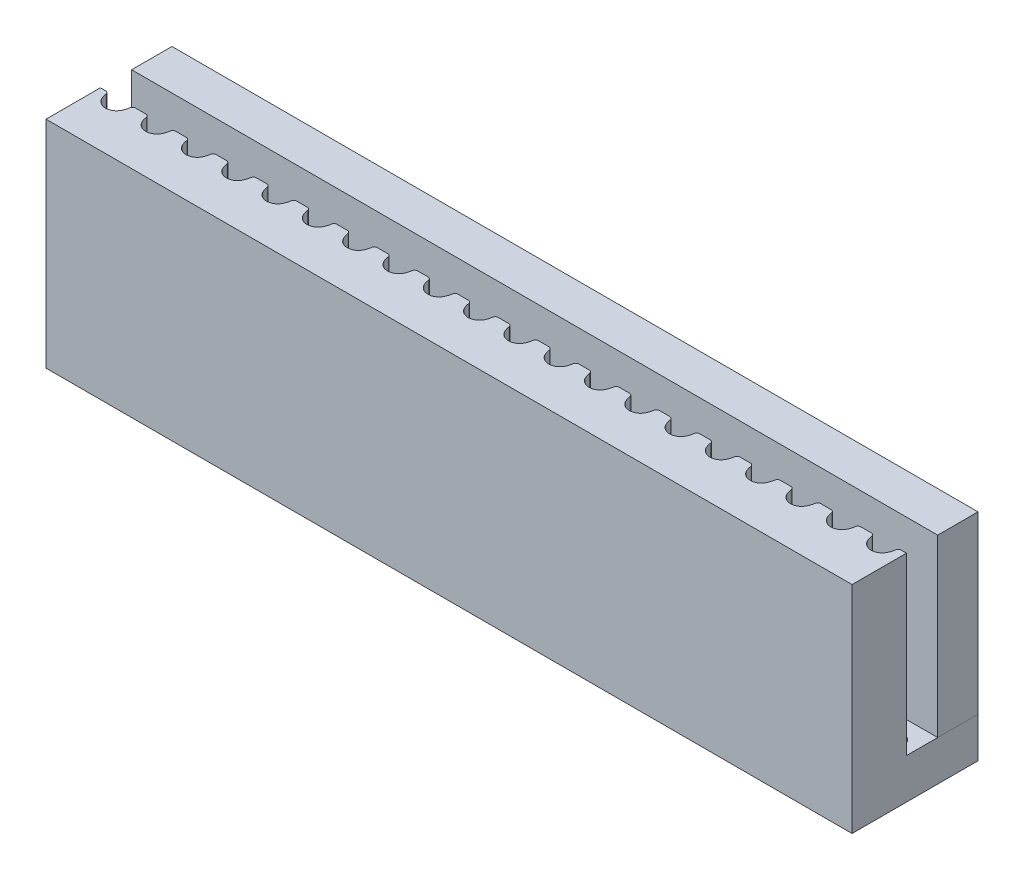
SolidWorks part; units mm, degrees
ref_plane "Front Plane" through (0, 0, 0) normal (0, 0, 1) x (1, 0, 0)
ref_plane "Top Plane" through (0, 0, 0) normal (0, 1, 0) x (1, 0, 0)
ref_plane "Right Plane" through (0, 0, 0) normal (1, 0, 0) x (0, 0, -1)
sketch "Sketch1" plane through (0, 0, 0) normal (0, 1, 0) x (1, 0, 0)
  line L0 (-20, 0.95) -> (20, 0.95) construction
  line L1 (0, -55) -> (0, 55) construction
  line L2 (-55, 0) -> (55, 0) construction
  line L3 (-20, 0.32) -> (20, 0.32)
  line L4 (-20, -0.43) -> (20, -0.43) construction
  line L5 (-19, 1.863) -> (-19, -1.7327) construction
  line L6 (-18.6, 1.863) -> (-18.6, -1.7327) construction
  line L7 (-20.453, 0.574) -> (20.5239, 0.574) construction
  line L8 (-19.4, 1.863) -> (-19.4, -1.7327) construction
  line L11 (-19.5915, 0.1896) -> (-17.5915, 0.1896) construction
  line L12 (20, 0.32) -> (20, -2.38)
  line L13 (20, -2.38) -> (-20, -2.38)
  line L14 (-20, -2.38) -> (-20, 0.32)
  line L17 (20, 1.87) -> (-20, 1.87)
  line L18 (20, 1.87) -> (20, 3.87)
  line L19 (20, 3.87) -> (-20, 3.87)
  line L20 (-20, 1.87) -> (-20, 3.87)
  circle A0 centre (-19, 0.125) radius 0.555
  arc A3 (-19.5915, 0.1896) -> (-19.7402, 0.32) centre (-19.7402, 0.17) ccw
  arc A4 (-18.2598, 0.32) -> (-18.4085, 0.1896) centre (-18.2598, 0.17) ccw
  arc A5 (-19.5915, 0.1896) -> (-19.4989, -0.1182) centre (-18.6, 0.32) ccw
  arc A6 (-18.5011, -0.1182) -> (-18.4085, 0.1896) centre (-19.4, 0.32) ccw
  arc A7 (-17.5915, 0.1896) -> (-17.7402, 0.32) centre (-17.7402, 0.17) ccw
  arc A8 (-17.5915, 0.1896) -> (-17.4989, -0.1182) centre (-16.6, 0.32) ccw
  circle A9 centre (-17, 0.125) radius 0.555
  arc A10 (-16.2598, 0.32) -> (-16.4085, 0.1896) centre (-16.2598, 0.17) ccw
  arc A11 (-16.5011, -0.1182) -> (-16.4085, 0.1896) centre (-17.4, 0.32) ccw
  arc A12 (-15.5915, 0.1896) -> (-15.7402, 0.32) centre (-15.7402, 0.17) ccw
  arc A13 (-15.5915, 0.1896) -> (-15.4989, -0.1182) centre (-14.6, 0.32) ccw
  circle A14 centre (-15, 0.125) radius 0.555
  arc A15 (-14.2598, 0.32) -> (-14.4085, 0.1896) centre (-14.2598, 0.17) ccw
  arc A16 (-14.5011, -0.1182) -> (-14.4085, 0.1896) centre (-15.4, 0.32) ccw
  arc A17 (-13.5915, 0.1896) -> (-13.7402, 0.32) centre (-13.7402, 0.17) ccw
  arc A18 (-13.5915, 0.1896) -> (-13.4989, -0.1182) centre (-12.6, 0.32) ccw
  circle A19 centre (-13, 0.125) radius 0.555
  arc A20 (-12.2598, 0.32) -> (-12.4085, 0.1896) centre (-12.2598, 0.17) ccw
  arc A21 (-12.5011, -0.1182) -> (-12.4085, 0.1896) centre (-13.4, 0.32) ccw
  arc A22 (-11.5915, 0.1896) -> (-11.7402, 0.32) centre (-11.7402, 0.17) ccw
  arc A23 (-11.5915, 0.1896) -> (-11.4989, -0.1182) centre (-10.6, 0.32) ccw
  circle A24 centre (-11, 0.125) radius 0.555
  arc A25 (-10.2598, 0.32) -> (-10.4085, 0.1896) centre (-10.2598, 0.17) ccw
  arc A26 (-10.5011, -0.1182) -> (-10.4085, 0.1896) centre (-11.4, 0.32) ccw
  arc A27 (-9.5915, 0.1896) -> (-9.7402, 0.32) centre (-9.7402, 0.17) ccw
  arc A28 (-9.5915, 0.1896) -> (-9.4989, -0.1182) centre (-8.6, 0.32) ccw
  circle A29 centre (-9, 0.125) radius 0.555
  arc A30 (-8.2598, 0.32) -> (-8.4085, 0.1896) centre (-8.2598, 0.17) ccw
  arc A31 (-8.5011, -0.1182) -> (-8.4085, 0.1896) centre (-9.4, 0.32) ccw
  arc A32 (-7.5915, 0.1896) -> (-7.7402, 0.32) centre (-7.7402, 0.17) ccw
  arc A33 (-7.5915, 0.1896) -> (-7.4989, -0.1182) centre (-6.6, 0.32) ccw
  circle A34 centre (-7, 0.125) radius 0.555
  arc A35 (-6.2598, 0.32) -> (-6.4085, 0.1896) centre (-6.2598, 0.17) ccw
  arc A36 (-6.5011, -0.1182) -> (-6.4085, 0.1896) centre (-7.4, 0.32) ccw
  arc A37 (-5.5915, 0.1896) -> (-5.7402, 0.32) centre (-5.7402, 0.17) ccw
  arc A38 (-5.5915, 0.1896) -> (-5.4989, -0.1182) centre (-4.6, 0.32) ccw
  circle A39 centre (-5, 0.125) radius 0.555
  arc A40 (-4.2598, 0.32) -> (-4.4085, 0.1896) centre (-4.2598, 0.17) ccw
  arc A41 (-4.5011, -0.1182) -> (-4.4085, 0.1896) centre (-5.4, 0.32) ccw
  arc A42 (-3.5915, 0.1896) -> (-3.7402, 0.32) centre (-3.7402, 0.17) ccw
  arc A43 (-3.5915, 0.1896) -> (-3.4989, -0.1182) centre (-2.6, 0.32) ccw
  circle A44 centre (-3, 0.125) radius 0.555
  arc A45 (-2.2598, 0.32) -> (-2.4085, 0.1896) centre (-2.2598, 0.17) ccw
  arc A46 (-2.5011, -0.1182) -> (-2.4085, 0.1896) centre (-3.4, 0.32) ccw
  arc A47 (-1.5915, 0.1896) -> (-1.7402, 0.32) centre (-1.7402, 0.17) ccw
  arc A48 (-1.5915, 0.1896) -> (-1.4989, -0.1182) centre (-0.6, 0.32) ccw
  circle A49 centre (-1, 0.125) radius 0.555
  arc A50 (-0.2598, 0.32) -> (-0.4085, 0.1896) centre (-0.2598, 0.17) ccw
  arc A51 (-0.5011, -0.1182) -> (-0.4085, 0.1896) centre (-1.4, 0.32) ccw
  arc A52 (0.4085, 0.1896) -> (0.2598, 0.32) centre (0.2598, 0.17) ccw
  arc A53 (0.4085, 0.1896) -> (0.5011, -0.1182) centre (1.4, 0.32) ccw
  circle A54 centre (1, 0.125) radius 0.555
  arc A55 (1.7402, 0.32) -> (1.5915, 0.1896) centre (1.7402, 0.17) ccw
  arc A56 (1.4989, -0.1182) -> (1.5915, 0.1896) centre (0.6, 0.32) ccw
  arc A57 (2.4085, 0.1896) -> (2.2598, 0.32) centre (2.2598, 0.17) ccw
  arc A58 (2.4085, 0.1896) -> (2.5011, -0.1182) centre (3.4, 0.32) ccw
  circle A59 centre (3, 0.125) radius 0.555
  arc A60 (3.7402, 0.32) -> (3.5915, 0.1896) centre (3.7402, 0.17) ccw
  arc A61 (3.4989, -0.1182) -> (3.5915, 0.1896) centre (2.6, 0.32) ccw
  arc A62 (4.4085, 0.1896) -> (4.2598, 0.32) centre (4.2598, 0.17) ccw
  arc A63 (4.4085, 0.1896) -> (4.5011, -0.1182) centre (5.4, 0.32) ccw
  circle A64 centre (5, 0.125) radius 0.555
  arc A65 (5.7402, 0.32) -> (5.5915, 0.1896) centre (5.7402, 0.17) ccw
  arc A66 (5.4989, -0.1182) -> (5.5915, 0.1896) centre (4.6, 0.32) ccw
  arc A67 (6.4085, 0.1896) -> (6.2598, 0.32) centre (6.2598, 0.17) ccw
  arc A68 (6.4085, 0.1896) -> (6.5011, -0.1182) centre (7.4, 0.32) ccw
  circle A69 centre (7, 0.125) radius 0.555
  arc A70 (7.7402, 0.32) -> (7.5915, 0.1896) centre (7.7402, 0.17) ccw
  arc A71 (7.4989, -0.1182) -> (7.5915, 0.1896) centre (6.6, 0.32) ccw
  arc A72 (8.4085, 0.1896) -> (8.2598, 0.32) centre (8.2598, 0.17) ccw
  arc A73 (8.4085, 0.1896) -> (8.5011, -0.1182) centre (9.4, 0.32) ccw
  circle A74 centre (9, 0.125) radius 0.555
  arc A75 (9.7402, 0.32) -> (9.5915, 0.1896) centre (9.7402, 0.17) ccw
  arc A76 (9.4989, -0.1182) -> (9.5915, 0.1896) centre (8.6, 0.32) ccw
  arc A77 (10.4085, 0.1896) -> (10.2598, 0.32) centre (10.2598, 0.17) ccw
  arc A78 (10.4085, 0.1896) -> (10.5011, -0.1182) centre (11.4, 0.32) ccw
  circle A79 centre (11, 0.125) radius 0.555
  arc A80 (11.7402, 0.32) -> (11.5915, 0.1896) centre (11.7402, 0.17) ccw
  arc A81 (11.4989, -0.1182) -> (11.5915, 0.1896) centre (10.6, 0.32) ccw
  arc A82 (12.4085, 0.1896) -> (12.2598, 0.32) centre (12.2598, 0.17) ccw
  arc A83 (12.4085, 0.1896) -> (12.5011, -0.1182) centre (13.4, 0.32) ccw
  circle A84 centre (13, 0.125) radius 0.555
  arc A85 (13.7402, 0.32) -> (13.5915, 0.1896) centre (13.7402, 0.17) ccw
  arc A86 (13.4989, -0.1182) -> (13.5915, 0.1896) centre (12.6, 0.32) ccw
  arc A87 (14.4085, 0.1896) -> (14.2598, 0.32) centre (14.2598, 0.17) ccw
  arc A88 (14.4085, 0.1896) -> (14.5011, -0.1182) centre (15.4, 0.32) ccw
  circle A89 centre (15, 0.125) radius 0.555
  arc A90 (15.7402, 0.32) -> (15.5915, 0.1896) centre (15.7402, 0.17) ccw
  arc A91 (15.4989, -0.1182) -> (15.5915, 0.1896) centre (14.6, 0.32) ccw
  arc A92 (16.4085, 0.1896) -> (16.2598, 0.32) centre (16.2598, 0.17) ccw
  arc A93 (16.4085, 0.1896) -> (16.5011, -0.1182) centre (17.4, 0.32) ccw
  circle A94 centre (17, 0.125) radius 0.555
  arc A95 (17.7402, 0.32) -> (17.5915, 0.1896) centre (17.7402, 0.17) ccw
  arc A96 (17.4989, -0.1182) -> (17.5915, 0.1896) centre (16.6, 0.32) ccw
  arc A97 (18.4085, 0.1896) -> (18.2598, 0.32) centre (18.2598, 0.17) ccw
  arc A98 (18.4085, 0.1896) -> (18.5011, -0.1182) centre (19.4, 0.32) ccw
  circle A99 centre (19, 0.125) radius 0.555
  arc A100 (19.7402, 0.32) -> (19.5915, 0.1896) centre (19.7402, 0.17) ccw
  arc A101 (19.4989, -0.1182) -> (19.5915, 0.1896) centre (18.6, 0.32) ccw
  point P2 (0, 0.95)
  dimension "D6" = 1.11
  dimension "D9" = 20
  dimension "D11" = 2
  dimension "D12" = 0.3
  dimension "D1" = 0.95
  dimension "D2" = 40
  dimension "D3" = 0.63
  dimension "D4" = 1.38
  dimension "D5" = 1
  dimension "D7" = 0.4
  dimension "D8" = 0.254
  dimension "D10" = 0.4
  dimension "D13" = 2.3
  dimension "D14" = 2
  dimension "D15" = 2.7
extrude "Boss-Extrude1" add sketch "Sketch1" along normal blind 8.7
sketch "Sketch2" plane through (0, 0, 0) normal (0, -1, 0) x (1, 0, 0)
  line L5 (-20, -1.87) -> (-20, -3.87) construction
  line L6 (-20, -3.87) -> (20, -3.87)
  line L7 (-17, -0.67) -> (-15, -0.67) construction
  line L8 (-17, -0.67) -> (-19, -0.67) construction
  line L9 (-20, -3.87) -> (-20, 2.38)
  line L10 (-20, 2.38) -> (20, 2.38)
  line L11 (20, -3.87) -> (20, 2.38)
  circle A0 centre (-17, -0.67) radius 0.5
  circle A1 centre (-15, -0.67) radius 0.5
  circle A2 centre (-13, -0.67) radius 0.5
  circle A3 centre (-11, -0.67) radius 0.5
  circle A4 centre (-9, -0.67) radius 0.5
  circle A5 centre (-7, -0.67) radius 0.5
  circle A6 centre (-5, -0.67) radius 0.5
  circle A7 centre (-3, -0.67) radius 0.5
  circle A8 centre (-1, -0.67) radius 0.5
  circle A9 centre (1, -0.67) radius 0.5
  circle A10 centre (3, -0.67) radius 0.5
  circle A11 centre (5, -0.67) radius 0.5
  circle A12 centre (7, -0.67) radius 0.5
  circle A13 centre (9, -0.67) radius 0.5
  circle A14 centre (11, -0.67) radius 0.5
  circle A15 centre (13, -0.67) radius 0.5
  circle A16 centre (15, -0.67) radius 0.5
  circle A17 centre (17, -0.67) radius 0.5
  circle A18 centre (19, -0.67) radius 0.5
  circle A20 centre (-19, -0.67) radius 0.5
  arc A21 (-16.5011, 0.1182) -> (-17.4989, 0.1182) centre (-17, -0.125) ccw construction
  circle A22 centre (21, -0.67) radius 0.5 [skipped]
  point P1 (20, -3.87)
  point P13 (0, 0)
  point P14 (-17, 0.43)
  point P60 (20, 1.13)
  point P61 (20, 1.13)
  point P66 (0, 0)
  dimension "D1" = 1
  dimension "D2" = 1.1
  dimension "D4" = 2
  dimension "D6" = 2
  dimension "D3" = 20
  dimension "D5" = 2
extrude "Boss-Extrude2" add sketch "Sketch2" along normal blind 2
